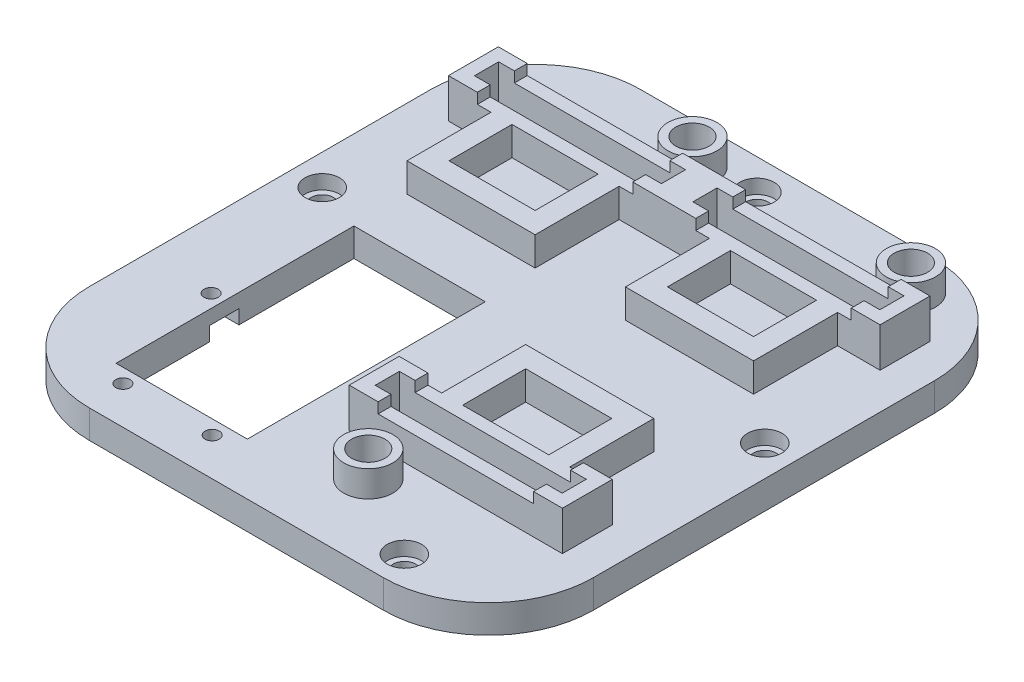
SolidWorks part; units mm, degrees
material "ABS"
ref_plane "Front Plane" through (0, 0, 0) normal (0, 0, 1) x (1, 0, 0)
ref_plane "Top Plane" through (0, 0, 0) normal (0, 1, 0) x (1, 0, 0)
ref_plane "Right Plane" through (0, 0, 0) normal (1, 0, 0) x (0, 0, -1)
sketch "Sketch1" plane through (0, 0, 0) normal (0, 1, 0) x (1, 0, 0)
  line L0 (-48, 0) -> (48, 0) construction
  line L1 (0, 50) -> (0, -55) construction
  line L2 (-38.6, 19.5) -> (-3, 19.5) construction
  line L3 (-38.6, 50.5) -> (-3, 50.5) construction
  line L4 (-38.6, 50.5) -> (-38.6, 15) construction
  line L5 (-38.6, 15) -> (-3, 15) construction
  line L6 (-38.6, 46) -> (-3, 46) construction
  line L7 (38.6, 15) -> (3, 50.5) construction
  line L8 (38.6, 50.5) -> (3, 15) construction
  line L9 (-3, 50.5) -> (-3, 15) construction
  line L10 (-38.6, 50.5) -> (-3, 15) construction
  line L11 (-38.6, 15) -> (-3, 50.5) construction
  line L12 (3, 50.5) -> (3, 15) construction
  line L13 (38.6, 46) -> (3, 46) construction
  line L14 (38.6, 15) -> (3, 15) construction
  line L15 (38.6, 50.5) -> (38.6, 15) construction
  line L16 (38.6, 50.5) -> (3, 50.5) construction
  line L17 (38.6, 19.5) -> (3, 19.5) construction
  line L18 (38.6, -19.5) -> (3, -19.5) construction
  line L19 (38.6, -50.5) -> (3, -50.5) construction
  line L20 (38.6, -50.5) -> (38.6, -15) construction
  line L21 (38.6, -15) -> (3, -15) construction
  line L22 (38.6, -46) -> (3, -46) construction
  line L23 (3, -50.5) -> (3, -15) construction
  line L24 (38.6, -50.5) -> (3, -15) construction
  line L25 (38.6, -15) -> (3, -50.5) construction
  line L26 (-38.1, 0) -> (-38.1, -50.6) construction
  line L27 (-38.1, -50.6) -> (-2.5, -50.6) construction
  line L28 (-2.5, -50.6) -> (-2.5, 0) construction
  line L29 (-2.5, 0) -> (-38.1, 0) construction
  line L30 (-48, -35) -> (-48, 30)
  line L31 (-28, 50) -> (28, 50)
  line L32 (48, 30) -> (48, -35)
  line L33 (28, -55) -> (-28, -55)
  line L34 (20.8, -50.5) -> (20.8, -15) construction
  line L35 (20.8, 15) -> (20.8, 50.5) construction
  line L36 (-20.8, 15) -> (-20.8, 50.5) construction
  line L37 (-33.38, 15) -> (-33.38, 6.08) construction
  line L38 (-33.38, 6.08) -> (-8.22, 6.08) construction
  line L39 (-8.22, 6.08) -> (-8.22, 15) construction
  line L40 (8.22, 6.08) -> (8.22, 15) construction
  line L41 (33.38, 6.08) -> (8.22, 6.08) construction
  line L42 (33.38, 15) -> (33.38, 6.08) construction
  line L43 (33.38, -15) -> (33.38, -6.08) construction
  line L44 (33.38, -6.08) -> (8.22, -6.08) construction
  line L45 (8.22, -6.08) -> (8.22, -15) construction
  arc A0 (48, -35) -> (28, -55) centre (28, -35) cw
  arc A1 (48, 30) -> (28, 50) centre (28, 30) ccw
  arc A2 (-48, 30) -> (-28, 50) centre (-28, 30) cw
  arc A3 (-28, -55) -> (-48, -35) centre (-28, -35) cw
  point P8 (-20.8, 32.75)
  point P21 (20.8, 32.75)
  point P30 (20.8, -32.75)
  dimension "D1" = 35.6
  dimension "D14" = 20
  dimension "D2" = 35.5
  dimension "D3" = 4.5
  dimension "D4" = 3
  dimension "D5" = 35.6
  dimension "D6" = 50.6
  dimension "D7" = 15
  dimension "D8" = 4.5
  dimension "D9" = 2.5
  dimension "D10" = 48
  dimension "D11" = 48
  dimension "D12" = 50
  dimension "D13" = 55
  dimension "D15" = 8.92
  dimension "D16" = 25.16
  dimension "D17" = 12.58
extrude "w_top" add sketch "Sketch1" along normal blind 3.175
extrude "a_holders" add sketch "Sketch3" along normal blind 5.5 from surface at 0 starting at face at (0, 3.175, 2.5)
sketch "Sketch3" plane through (0, 3.175, 0) normal (0, 1, 0) x (1, 0, 0)
  line L0 (3, -29.25) -> (38.6, -29.25) construction
  line L1 (20.8, -34) -> (20.8, -8.5) construction
  line L2 (-48, 0) -> (48, 0) construction
  line L4 (12.6, -24.5) -> (29, -24.5)
  line L5 (-41.1, 31.25) -> (41.1, 31.25) construction
  line L6 (-20.8, 10.5) -> (-20.8, 36) construction
  line L7 (29, -12.5) -> (29, -24.5)
  line L8 (12.6, -12.5) -> (29, -12.5)
  line L9 (12.6, -24.5) -> (12.6, -12.5)
  line L10 (0.5, -24.5) -> (0.5, -34)
  line L11 (8.6, -24.5) -> (8.6, -8.5)
  line L12 (8.6, -8.5) -> (33, -8.5)
  line L13 (33, -8.5) -> (33, -24.5)
  line L14 (41.1, -24.5) -> (33, -24.5)
  line L15 (41.1, -34) -> (41.1, -24.5)
  line L16 (0.5, -34) -> (41.1, -34)
  line L17 (3, -31.55) -> (38.6, -31.55)
  line L18 (38.6, -31.55) -> (38.6, -26.95)
  line L23 (38.6, -26.95) -> (3, -26.95)
  line L25 (3, -31.55) -> (3, -26.95)
  line L26 (8.6, -24.5) -> (0.5, -24.5)
  line L40 (48, 30) -> (48, -35) construction
  line L41 (28, -55) -> (-28, -55) construction
  line L58 (-38.6, 28.95) -> (-38.6, 33.55) construction
  line L59 (20.8, 36) -> (20.8, 10.5) construction
  line L60 (8.6, 26.5) -> (-8.6, 26.5)
  line L61 (12.6, 26.5) -> (29, 26.5)
  line L62 (-33, 26.5) -> (-41.1, 26.5)
  line L63 (-29, 26.5) -> (-12.6, 26.5)
  line L64 (29, 14.5) -> (29, 26.5)
  line L65 (12.6, 14.5) -> (29, 14.5)
  line L66 (-41.1, 36) -> (41.1, 36)
  line L67 (41.1, 36) -> (41.1, 26.5)
  line L68 (41.1, 26.5) -> (33, 26.5)
  line L69 (12.6, 26.5) -> (12.6, 14.5)
  line L70 (-41.1, 26.5) -> (-41.1, 36)
  line L71 (-38.6, 33.55) -> (-3, 33.55)
  line L72 (33, 10.5) -> (33, 26.5)
  line L73 (8.6, 10.5) -> (33, 10.5)
  line L74 (8.6, 26.5) -> (8.6, 10.5)
  line L75 (-12.6, 14.5) -> (-12.6, 26.5)
  line L76 (-29, 14.5) -> (-12.6, 14.5)
  line L77 (-8.6, 10.5) -> (-8.6, 26.5)
  line L78 (38.6, 33.55) -> (38.6, 28.95)
  line L79 (38.6, 28.95) -> (3, 28.95)
  line L80 (-38.6, 28.95) -> (-38.6, 33.55)
  line L81 (-3, 33.55) -> (-3, 28.95)
  line L82 (3, 33.55) -> (3, 28.95)
  line L83 (-33, 10.5) -> (-8.6, 10.5)
  line L84 (-33, 26.5) -> (-33, 10.5)
  line L85 (-29, 26.5) -> (-29, 14.5)
  line L86 (-3, 28.95) -> (-38.6, 28.95)
  line L87 (3, 33.55) -> (38.6, 33.55)
  point P0 (-38.6, 50.5)
  point P1 (49.6897, 50.5)
  point P2 (3, 31.25)
  point P3 (49.6897, 45.9)
  point P4 (-38.6, 45.9)
  point P42 (0.5, -85.5)
  point P45 (41.1, -85.5)
  dimension "D4" = 4.6
  dimension "D3" = 35.6
  dimension "D5" = 9.5
  dimension "D6" = 17.2
  dimension "D7" = 40.6
  dimension "D8" = 8.5
  dimension "D9" = 4
  dimension "D10" = 4
  dimension "D11" = 2.45
  dimension "D12" = 2.5
  dimension "D13" = 2.45
  dimension "D14" = 16
  dimension "D15" = 8.1
  dimension "D16" = 4.6
  dimension "D18" = 2.5
  dimension "D19" = 16.4
  dimension "D17" = 12
  dimension "D20" = 24.4
  dimension "D21" = 82.2
  dimension "D22" = 10.5
  dimension "D23" = 25.5
  dimension "D24" = 9.5
  dimension "D25" = 0.5
  dimension "D26" = 6
  dimension "D31" = 2.5
  dimension "D32" = 4
  dimension "D33" = 4
sketch "Sketch14" plane through (0, 8.675, 0) normal (0, 1, 0) x (1, 0, 0)
  line L0 (-35.6, 33.55) -> (-35.6, 36)
  line L1 (6, -24.5) -> (0.5, -24.5)
  line L2 (0.5, -24.5) -> (8.6, -24.5) construction
  line L3 (-35.6, 36) -> (-41.1, 36)
  line L4 (-41.1, 36) -> (-41.1, 26.5)
  line L5 (-41.1, 26.5) -> (-35.6, 26.5)
  line L6 (0.5, -24.5) -> (0.5, -34)
  line L7 (-35.6, 26.5) -> (-35.6, 28.95)
  line L8 (0.5, -34) -> (6, -34)
  line L9 (-35.6, 28.95) -> (-38.6, 28.95)
  line L10 (-38.6, 28.95) -> (-38.6, 33.55)
  line L11 (-38.6, 33.55) -> (-35.6, 33.55)
  line L12 (0, 0) -> (0, 50) construction
  line L13 (-28, 50) -> (28, 50) construction
  line L14 (0, 0) -> (48, 0) construction
  line L15 (48, 30) -> (48, -35) construction
  line L16 (-20.8, 10.5) -> (-20.8, 36) construction
  line L18 (6, -34) -> (6, -31.55)
  line L19 (-3, 33.55) -> (-6, 33.55)
  line L20 (-3, 28.95) -> (-3, 33.55)
  line L21 (-6, 28.95) -> (-3, 28.95)
  line L22 (-6, 26.5) -> (-6, 28.95)
  line L23 (-6, 36) -> (6, 36)
  line L24 (-6, 26.5) -> (6, 26.5)
  line L26 (-6, 33.55) -> (-6, 36)
  line L27 (6, 33.55) -> (6, 36)
  line L28 (-38.6, 33.55) -> (-3, 33.55) construction
  line L29 (-3, 28.95) -> (-38.6, 28.95) construction
  line L31 (6, 26.5) -> (6, 28.95)
  line L32 (6, 28.95) -> (3, 28.95)
  line L33 (3, 28.95) -> (3, 33.55)
  line L34 (3, 33.55) -> (6, 33.55)
  line L35 (38.6, 33.55) -> (35.6, 33.55)
  line L36 (38.6, 28.95) -> (38.6, 33.55)
  line L37 (35.6, 28.95) -> (38.6, 28.95)
  line L38 (35.6, 26.5) -> (35.6, 28.95)
  line L39 (41.1, 26.5) -> (35.6, 26.5)
  line L40 (41.1, 36) -> (41.1, 26.5)
  line L41 (35.6, 36) -> (41.1, 36)
  line L42 (35.6, 33.55) -> (35.6, 36)
  line L43 (38.6, -31.55) -> (3, -31.55) construction
  line L44 (-33, 26.5) -> (-41.1, 26.5) construction
  line L45 (3, -26.95) -> (6, -26.95)
  line L46 (3, -31.55) -> (3, -26.95)
  line L47 (3, -31.55) -> (6, -31.55)
  line L48 (-33, 26.5) -> (-41.1, 26.5) construction
  line L49 (-41.1, 36) -> (41.1, 36) construction
  line L50 (3, -26.95) -> (38.6, -26.95) construction
  line L51 (6, -26.95) -> (6, -24.5)
  line L52 (41.1, -34) -> (0.5, -34) construction
  line L53 (8.6, -8.5) -> (33, -8.5) construction
  line L54 (20.8, -34) -> (20.8, -8.5) construction
  line L55 (41.1, -34) -> (0.5, -34) construction
  line L57 (35.6, -26.95) -> (35.6, -24.5)
  line L58 (38.6, -31.55) -> (35.6, -31.55)
  line L59 (-8.6, 10.5) -> (-33, 10.5) construction
  line L60 (38.6, -31.55) -> (38.6, -26.95)
  line L61 (38.6, -26.95) -> (35.6, -26.95)
  line L62 (0.5, -24.5) -> (8.6, -24.5) construction
  line L63 (35.6, -34) -> (35.6, -31.55)
  line L64 (41.1, -34) -> (35.6, -34)
  line L65 (41.1, -24.5) -> (41.1, -34)
  line L66 (35.6, -24.5) -> (41.1, -24.5)
  dimension "D1" = 5.5
  dimension "D2" = 2.5
extrude "a_clamp" add sketch "Sketch14" along normal blind 2
sketch "Sketch12" plane through (0, 3.175, 0) normal (0, 1, 0) x (1, 0, 0)
  line L0 (-38.1, 0) -> (-2.5, 0) construction
  line L1 (-2.5, 0) -> (-2.5, -50.6) construction
  line L2 (-2.5, -50.6) -> (-38.1, -50.6) construction
  line L3 (-38.1, -50.6) -> (-38.1, 0) construction
  line L4 (-20.3, 0) -> (-20.3, -50.6) construction
  line L5 (-38.1, -12) -> (-2.5, -12) construction
  line L6 (-32.5, 0) -> (-32.5, -45) construction
  line L7 (-8.1, 0) -> (-8.1, -45) construction
  line L8 (-32.5, -45) -> (-8.1, -45) construction
  line L9 (-35.3, -47.8) -> (-5.3, -47.8) construction
  line L10 (-35.3, -47.8) -> (-35.3, 0) construction
  line L11 (-5.3, 0) -> (-5.3, -47.8) construction
  line L12 (-35.3, -24.5) -> (-5.3, -24.5) construction
  line L13 (-32.8, 0.2) -> (-32.8, -45.1)
  line L14 (-32.8, -45.1) -> (-7.8, -45.1)
  line L15 (-7.8, -45.1) -> (-7.8, 0.2)
  line L16 (-32.8, 0.2) -> (-7.8, 0.2)
  circle A0 centre (-20.3, -12) radius 11.03 construction
  circle A1 centre (-28.8, -47.8) radius 1.35
  circle A2 centre (-11.8, -47.8) radius 1.35
  circle A3 centre (-20.3, -12) radius 12.57 construction
  circle A4 centre (-35.3, -24.5) radius 1.35
  circle A5 centre (-5.3, -24.5) radius 1.35
  circle A6 centre (-20.3, -12) radius 12 construction
  dimension "D1" = 12
  dimension "D2" = 22.06
  dimension "D9" = 2.7
  dimension "D10" = 8.5
  dimension "D11" = 8.5
  dimension "D12" = 12.5
  dimension "D13" = 0.3
  dimension "D14" = 0.3
  dimension "D17" = 25.14
  dimension "D18" = 24
  dimension "D3" = 5.6
  dimension "D4" = 5.6
  dimension "D5" = 5.6
  dimension "D6" = 35.8
  dimension "D7" = 2.8
  dimension "D8" = 2.8
  dimension "D15" = 0.2
  dimension "D16" = 0.2
extrude "a_holes" cut sketch "Sketch12" against normal up to surface (3.175 mm away) up to face at (0, 0, 2.5)
sketch "Sketch13" plane through (0, 0, 0) normal (0, -1, 0) x (1, 0, 0)
  line L0 (-31.6, 47.8) -> (-31.6, 45.1)
  line L1 (-7.8, 45.1) -> (-32.8, 45.1) construction
  line L3 (-31.6, 45.1) -> (-26, 45.1)
  line L4 (-26, 45.1) -> (-26, 47.8)
  line L5 (-35.3, 27.3) -> (-32.8, 27.3)
  line L7 (-32.8, 27.3) -> (-32.8, 21.7)
  line L8 (-32.8, 21.7) -> (-35.3, 21.7)
  line L9 (-20.3, 45.1) -> (-20.3, -0.2) construction
  line L11 (-7.8, 21.7) -> (-5.3, 21.7)
  line L12 (-7.8, 27.3) -> (-7.8, 21.7)
  line L13 (-5.3, 27.3) -> (-7.8, 27.3)
  line L14 (-14.6, 45.1) -> (-14.6, 47.8)
  line L15 (-9, 45.1) -> (-14.6, 45.1)
  line L16 (-9, 47.8) -> (-9, 45.1)
  line L17 (-32.8, 45.1) -> (-32.8, -0.2) construction
  line L18 (-32.8, -0.2) -> (-7.8, -0.2) construction
  arc A0 (-26, 47.8) -> (-31.6, 47.8) centre (-28.8, 47.8) ccw
  arc A1 (-5.3, 27.3) -> (-5.3, 21.7) centre (-5.3, 24.5) cw
  arc A2 (-14.6, 47.8) -> (-9, 47.8) centre (-11.8, 47.8) cw
  arc A3 (-35.3, 27.3) -> (-35.3, 21.7) centre (-35.3, 24.5) ccw
extrude "a_holes guide" cut sketch "Sketch13" against normal blind 1.5 from offset 1
sketch "Sketch15" plane through (0, 3.175, 0) normal (0, 1, 0) x (1, 0, 0)
  line L0 (-38.6, 33.55) -> (-38.6, 42.17) construction
  line L1 (38.6, 33.55) -> (38.6, 28.95) construction
  line L2 (-38.6, 42.17) -> (38.6, 42.17) construction
  line L3 (38.6, 42.17) -> (38.6, 33.55) construction
  line L5 (3, -31.55) -> (3, -40.17) construction
  line L6 (3, -40.17) -> (38.6, -40.17) construction
  line L7 (-35.6, 33.55) -> (-35.6, 42.17) construction
  line L8 (35.6, -31.55) -> (35.6, -34) construction
  line L9 (38.6, -40.17) -> (38.6, -31.55) construction
  line L10 (0, 0) -> (0, 50) construction
  line L11 (-28, 50) -> (28, 50) construction
  line L12 (0, 0) -> (48, 0) construction
  line L13 (-20.8, 10.5) -> (-20.8, 36) construction
  line L14 (48, 30) -> (48, -35) construction
  line L15 (-8.6, 10.5) -> (-33, 10.5) construction
  line L16 (-35.6, 36) -> (-6, 36) construction
  line L17 (20.8, 10.5) -> (20.8, 33.55) construction
  line L18 (35.6, 33.55) -> (35.6, 42.17) construction
  line L20 (6, 33.55) -> (35.6, 33.55) construction
  line L21 (20.8, -31.55) -> (20.8, -8.5) construction
  line L22 (35.6, -31.55) -> (6, -31.55) construction
  line L24 (-41.1, 36) -> (41.1, 36) construction
  line L25 (8.6, -8.5) -> (33, -8.5) construction
  line L26 (35.6, -34) -> (6, -34) construction
  line L27 (33, 10.5) -> (8.6, 10.5) construction
  circle A0 centre (31.3, 42.17) radius 1.75 construction
  circle A1 centre (-31.3, 42.17) radius 1.75 construction
  circle A2 centre (31.3, -40.17) radius 1.75 construction
  circle A3 centre (-10.3, 42.17) radius 1.75 construction
  circle A4 centre (10.3, 42.17) radius 1.75 construction
  circle A5 centre (10.3, -40.17) radius 1.75 construction
  circle A6 centre (-10.3, 42.17) radius 3.175
  circle A7 centre (31.3, 42.17) radius 3.175
  circle A8 centre (10.3, -40.17) radius 3.175
  dimension "D5" = 3.5
  dimension "D2" = 4.3
  dimension "D4" = 4.3
  dimension "D7" = 6.35
  dimension "D1" = 6.17
  dimension "D3" = 6.17
  dimension "D6" = 4.3
extrude "tendon holes" cut sketch "Sketch15" against normal up to surface (3.175 mm away) up to face at (-20.3, 0, 33.15)
sketch "Sketch16" plane through (0, 3.175, 0) normal (0, 1, 0) x (1, 0, 0)
  circle A0 centre (-10.3, 42.17) radius 4.675
  circle A1 centre (-10.3, 42.17) radius 3.175 construction
  circle A2 centre (31.3, 42.17) radius 4.675
  circle A3 centre (10.3, -40.17) radius 4.675
  circle A4 centre (31.3, 42.17) radius 3.175 construction
  circle A5 centre (10.3, -40.17) radius 3.175 construction
  circle A6 centre (-10.3, 42.17) radius 3.175
  circle A7 centre (31.3, 42.17) radius 3.175
  circle A8 centre (10.3, -40.17) radius 3.175
  dimension "D1" = 1.5
  dimension "D2" = 1.5
  dimension "D3" = 1.5
extrude "tube_support" add sketch "Sketch16" along normal blind 5
sketch "Sketch19" plane through (0, 0, 0) normal (0, -1, 0) x (1, 0, 0)
  line L0 (-48, -30) -> (-48, 35)
  line L1 (-28, 55) -> (28, 55)
  line L2 (48, 35) -> (48, -30)
  line L3 (28, -50) -> (-28, -50)
  line L4 (-32.8, -0.2) -> (-7.8, -0.2)
  line L5 (-7.8, -0.2) -> (-7.8, 21.7)
  line L6 (-7.8, 27.3) -> (-5.3, 27.3)
  line L7 (-7.8, 27.3) -> (-7.8, 45.1)
  line L8 (-7.8, 45.1) -> (-9, 45.1)
  line L9 (-9, 45.1) -> (-9, 47.8)
  line L10 (-14.6, 45.1) -> (-14.6, 47.8)
  line L11 (-14.6, 45.1) -> (-26, 45.1)
  line L12 (-14.6, 45.1) -> (-26, 45.1) construction
  line L13 (-26, 47.8) -> (-26, 45.1)
  line L14 (-31.6, 47.8) -> (-31.6, 45.1)
  line L15 (-31.6, 45.1) -> (-32.8, 45.1)
  line L16 (-32.8, 45.1) -> (-32.8, 27.3)
  line L17 (-32.8, 27.3) -> (-35.3, 27.3)
  line L18 (-35.3, 21.7) -> (-32.8, 21.7)
  line L19 (-32.8, 21.7) -> (-32.8, -0.2)
  line L20 (-7.8, 21.7) -> (-5.3, 21.7)
  arc A0 (-48, 35) -> (-28, 55) centre (-28, 35) cw
  arc A1 (28, 55) -> (48, 35) centre (28, 35) cw
  arc A2 (48, -30) -> (28, -50) centre (28, -30) cw
  arc A3 (-28, -50) -> (-48, -30) centre (-28, -30) cw
  arc A4 (-35.3, 27.3) -> (-35.3, 21.7) centre (-35.3, 24.5) ccw
  arc A5 (-5.3, 27.3) -> (-5.3, 21.7) centre (-5.3, 24.5) cw
  arc A6 (-14.6, 47.8) -> (-9, 47.8) centre (-11.8, 47.8) cw
  arc A7 (-26, 47.8) -> (-31.6, 47.8) centre (-28.8, 47.8) ccw
  circle A8 centre (10.3, 40.17) radius 3.175
  circle A9 centre (-10.3, -42.17) radius 3.175
  circle A10 centre (31.3, -42.17) radius 3.175
  circle A11 centre (-10.3, -42.17) radius 3.175 construction
extrude "thickness compensation" add sketch "Sketch19" along normal blind 2.2
sketch "Sketch18" plane through (0, -2.2, 0) normal (0, -1, 0) x (1, 0, 0)
  line L0 (-20.3, 12) -> (-3.3294, -4.9706) construction
  line L1 (-38.1, 12) -> (-2.5, 12) construction
  line L2 (-3.3294, -4.9706) -> (10.3, 14.7839) construction
  line L3 (10.3, 40.17) -> (10.3, 14.7839) construction
  line L4 (10.5, -24.5855) -> (-3.3294, -4.9706) construction
  line L5 (-10.3, -42.17) -> (31.3, -42.17) construction
  line L6 (10.5, -42.17) -> (10.5, -24.5855) construction
  line L7 (10.3, 14.7839) -> (32.995, 22.59) construction
  circle A0 centre (-3.3294, -4.9706) radius 12 construction
  circle A1 centre (-20.3, 12) radius 12 construction
  circle A2 centre (32.995, 22.59) radius 12 construction
  circle A3 centre (10.5, -24.5855) radius 12 construction
  circle A4 centre (-3.3294, -4.9706) radius 5
  circle A7 centre (10.3, 14.7839) radius 12 construction
  circle A8 centre (10.3, 14.7839) radius 5
  circle A9 centre (32.995, 22.59) radius 5
  circle A10 centre (10.5, -24.5855) radius 5
  dimension "D1" = 45
  dimension "D2" = 17.5845
  dimension "D3" = 10
  dimension "D4" = 17.58
extrude "gear placements" cut sketch "Sketch18" against normal blind 1.25
sketch "Sketch20" plane through (0, -2.2, 0) normal (0, -1, 0) x (1, 0, 0)
  circle A0 centre (-42.1421, -3.5) radius 3.175 construction
  circle A1 centre (0, -44.1421) radius 3.175 construction
  circle A2 centre (42.1421, -3.5) radius 3.175 construction
  circle A3 centre (26.1421, 49.1421) radius 3.175 construction
  circle A4 centre (-42.1421, -3.5) radius 3.175
  circle A5 centre (0, -44.1421) radius 3.175
  circle A6 centre (42.1421, -3.5) radius 3.175
  circle A7 centre (26.1421, 49.1421) radius 3.175
  circle A8 centre (-42.1421, -3.5) radius 2.155
  circle A9 centre (0, -44.1421) radius 2.155
  circle A10 centre (42.1421, -3.5) radius 2.155
  circle A11 centre (26.1421, 49.1421) radius 2.155
  dimension "D1" = 4.31
extrude "screw holes" cut sketch "Sketch20" against normal up to surface (5.375 mm away) contours A8 | A9 | A10 | A11 up to face at (31.3, 3.175, -37.495)
sketch "Sketch21" plane through (0, 3.175, 0) normal (0, 1, 0) x (1, 0, 0)
  circle A0 centre (-42.1421, 3.5) radius 3.275
  circle A1 centre (42.1421, 3.5) radius 3.275
  circle A2 centre (0, 44.1421) radius 3.275
  circle A3 centre (26.1421, -49.1421) radius 3.275
  dimension "D1" = 6.55
extrude "standoff hole" cut sketch "Sketch21" against normal blind 2.7
